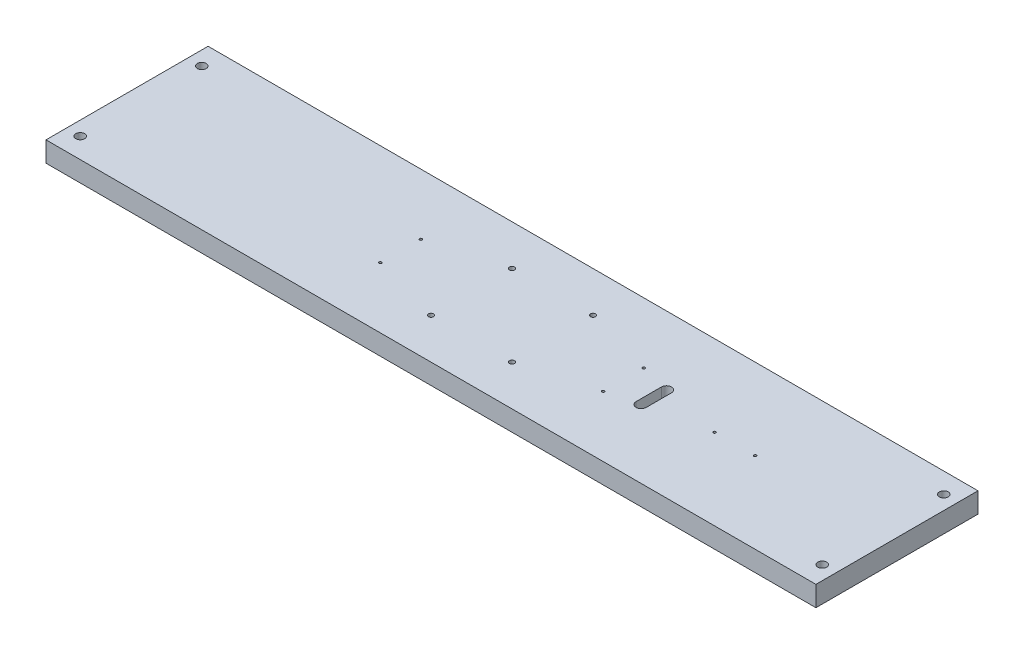
SolidWorks part; units mm, degrees
ref_plane "Front Plane" through (0, 0, 0) normal (0, 0, 1) x (1, 0, 0)
ref_plane "Top Plane" through (0, 0, 0) normal (0, 1, 0) x (1, 0, 0)
ref_plane "Right Plane" through (0, 0, 0) normal (1, 0, 0) x (0, 0, -1)
sketch "Sketch1" plane through (0, 0, 0) normal (0, 1, 0) x (1, 0, 0)
  line L1 (-241.3, -50.8) -> (241.3, -50.8)
  line L2 (-241.3, -50.8) -> (-241.3, 50.8)
  line L3 (-241.3, 50.8) -> (241.3, 50.8)
  line L4 (241.3, -50.8) -> (241.3, 50.8)
  line L5 (-241.3, -50.8) -> (241.3, 50.8) construction
  line L6 (-241.3, 50.8) -> (241.3, -50.8) construction
  point P0 (0, 0)
  dimension "D1" = 101.6
  dimension "D2" = 482.6
extrude "Boss-Extrude1" add sketch "Sketch1" along normal blind 12.7
sketch "Sketch2" plane through (0, 12.7, 0) normal (0, 1, 0) x (1, 0, 0)
  line L0 (0, 50.8) -> (0, -50.8) construction
  line L1 (241.3, 50.8) -> (-241.3, 50.8) construction
  line L2 (-241.3, -50.8) -> (241.3, -50.8) construction
  circle A0 centre (-232.5624, 38.1) radius 2.7813
  circle A1 centre (-232.5624, -38.1) radius 2.7813
  circle A2 centre (232.5624, 38.1) radius 2.7813
  circle A3 centre (232.5624, -38.1) radius 2.7813
  dimension "D1" = 465.1248
  dimension "D2" = 5.5626
  dimension "D3" = 5.5626
  dimension "D4" = 5.5626
  dimension "D5" = 5.5626
  dimension "D6" = 76.2
  dimension "D7" = 12.7
extrude "Cut-Extrude1" cut sketch "Sketch2" against normal through all
sketch "Sketch3" plane through (0, 12.7, 0) normal (0, 1, 0) x (1, 0, 0)
  line L1 (-25.4, -25.4) -> (25.4, -25.4) construction
  line L2 (-25.4, -25.4) -> (-25.4, 25.4) construction
  line L3 (-25.4, 25.4) -> (25.4, 25.4) construction
  line L4 (25.4, -25.4) -> (25.4, 25.4) construction
  line L5 (-25.4, -25.4) -> (25.4, 25.4) construction
  line L6 (-25.4, 25.4) -> (25.4, -25.4) construction
  circle A0 centre (-25.4, 25.4) radius 1.5875
  circle A1 centre (25.4, 25.4) radius 1.5875
  circle A2 centre (25.4, -25.4) radius 1.5875
  circle A3 centre (-25.4, -25.4) radius 1.5875
  point P0 (0, 0)
  dimension "D3" = 3.175
  dimension "D4" = 3.175
  dimension "D5" = 3.175
  dimension "D6" = 3.175
  dimension "D1" = 50.8
  dimension "D2" = 50.8
extrude "Cut-Extrude2" cut sketch "Sketch3" against normal through all
sketch "Sketch4" plane through (0, 12.7, 0) normal (0, 1, 0) x (1, 0, 0)
  line L0 (-241.3, 0) -> (241.3, 0) construction
  line L1 (-241.3, 50.8) -> (-241.3, -50.8) construction
  line L2 (241.3, -50.8) -> (241.3, 50.8) construction
  line L3 (0, 50.8) -> (0, -50.8) construction
  line L4 (241.3, 50.8) -> (-241.3, 50.8) construction
  line L5 (-241.3, -50.8) -> (241.3, -50.8) construction
  line L7 (-69.85, -12.7) -> (69.85, -12.7) construction
  line L8 (-69.85, -12.7) -> (-69.85, 12.7) construction
  line L9 (-69.85, 12.7) -> (69.85, 12.7) construction
  line L10 (69.85, -12.7) -> (69.85, 12.7) construction
  line L11 (-69.85, -12.7) -> (69.85, 12.7) construction
  line L12 (-69.85, 12.7) -> (69.85, -12.7) construction
  circle A4 centre (-69.85, 12.7) radius 0.7937
  circle A5 centre (-69.85, -12.7) radius 0.7937
  circle A6 centre (69.85, -12.7) radius 0.7937
  circle A7 centre (69.85, 12.7) radius 0.7937
  point P20 (0, 0)
  dimension "D11" = 1.5875
  dimension "D12" = 1.5875
  dimension "D13" = 1.5875
  dimension "D14" = 1.5875
  dimension "D9" = 25.4
  dimension "D10" = 139.7
extrude "Cut-Extrude3" cut sketch "Sketch4" against normal through all
sketch "Sketch5" plane through (0, 12.7, 0) normal (0, 1, 0) x (1, 0, 0)
  circle A0 centre (127, 0) radius 0.7938
  circle A1 centre (152.4, 0) radius 0.7937
  dimension "D2" = 1.5875
  dimension "D4" = 1.5875
  dimension "D1" = 25.4
  dimension "D3" = 127
extrude "Cut-Extrude4" cut sketch "Sketch5" against normal through all
sketch "Sketch6" plane through (0, 12.7, 0) normal (0, 1, 0) x (1, 0, 0)
  line L0 (0, 0) -> (88.9, 0) construction
  line L2 (88.9, 7.9375) -> (88.9, -7.9375) construction
  line L3 (85.725, 7.9375) -> (85.725, -7.9375)
  line L4 (92.075, 7.9375) -> (92.075, -7.9375)
  arc A3 (92.075, 7.9375) -> (85.725, 7.9375) centre (88.9, 7.9375) ccw
  arc A4 (85.725, -7.9375) -> (92.075, -7.9375) centre (88.9, -7.9375) ccw
  point P8 (0, 0)
  point P9 (0, 0)
  dimension "D2" = 15.875
  dimension "D1" = 88.9
  dimension "D3" = 6.35
extrude "Cut-Extrude5" cut sketch "Sketch6" against normal through all
